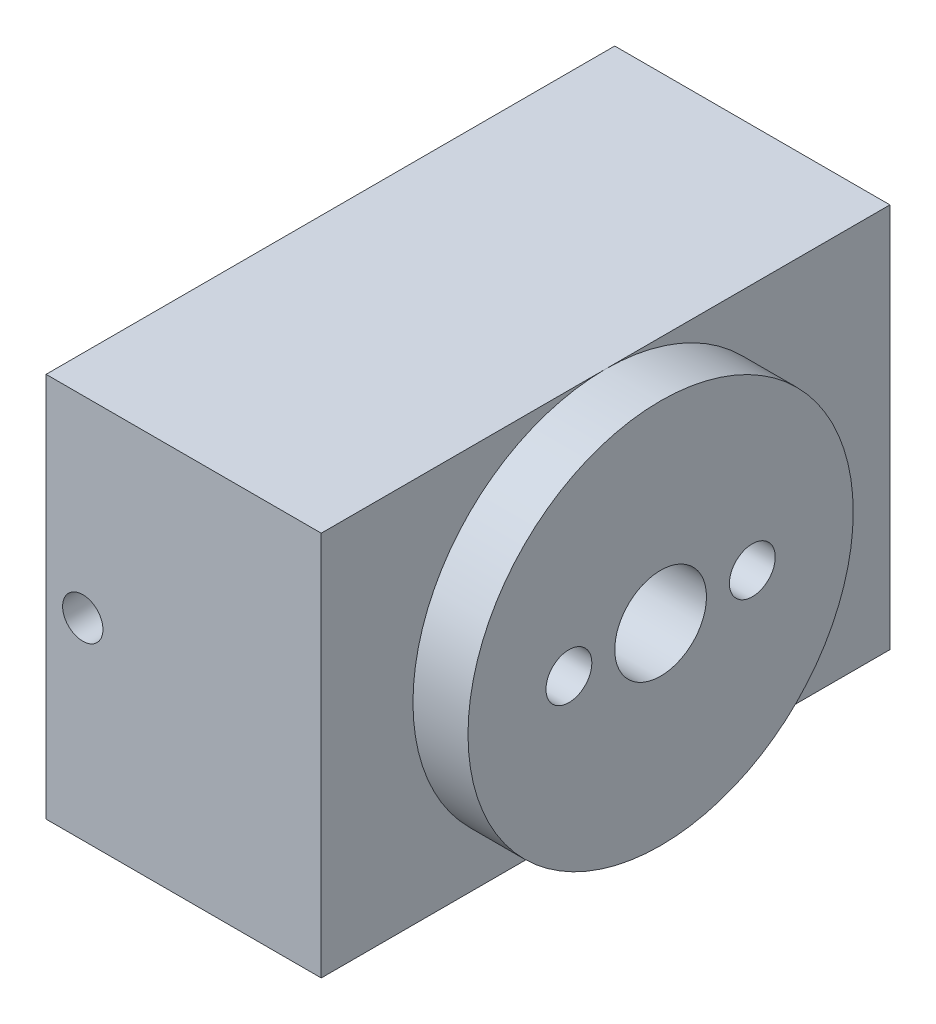
SolidWorks part; units mm, degrees
ref_plane "Front Plane" through (0, 0, 0) normal (0, 0, 1) x (1, 0, 0)
ref_plane "Top Plane" through (0, 0, 0) normal (0, 1, 0) x (1, 0, 0)
ref_plane "Right Plane" through (0, 0, 0) normal (1, 0, 0) x (0, 0, -1)
sketch "Sketch1" plane through (0, 0, 0) normal (1, 0, 0) x (0, 0, -1)
  line L0 (-15.5, 10.5) -> (15.5, 10.5)
  line L1 (-15.5, 10.5) -> (-15.5, -10.5)
  line L2 (-15.5, -10.5) -> (15.5, -10.5)
  line L3 (15.5, 10.5) -> (15.5, -10.5)
  dimension "D1" = 31
  dimension "D2" = 21
  dimension "D3" = 15.5
  dimension "D4" = 10.5
extrude "Boss-Extrude1" add sketch "Sketch1" along normal blind 15
sketch "Sketch4" plane through (0, 0, 15.5) normal (0, 0, 1) x (1, 0, 0)
  arc A0 (2.8122, 0.5833) -> (2.8122, -0.5833) centre (2, 0) ccw construction
  arc A1 (2.8122, 0.5833) -> (2.8122, -0.5833) centre (2, 0) ccw
  point P0 (2, 0)
hole_wizard "M2 Clearance Hole1" positions "Sketch4" profile "Sketch6" hole size "M2" standard "ANSI Metric" end condition through all
sketch "Sketch6" plane through (2, 0, 15.5) normal (1, 0, 0) x (0, -1, 0)
  line L0 (0, 0) -> (0, 31)
  line L1 (0, 31) -> (1.1, 31)
  line L2 (1.1, 31) -> (1.1, 0)
  line L5 (1.1, 0) -> (0, 0)
  line L11 (0, -6.35) -> (0, 107.95) construction
  dimension "Thru Hole Dia." = 2.2
  dimension "Thru Hole Depth" = 31
sketch "Sketch10" plane through (15, 0, 0) normal (1, 0, 0) x (0, 0, -1)
  circle A0 centre (0, 0) radius 10.5
extrude "Boss-Extrude3" add sketch "Sketch10" along normal blind 3
sketch "Sketch7" plane through (15, 0, 0) normal (1, 0, 0) x (0, 0, -1)
  circle A1 centre (-5, 0) radius 1.25
  circle A2 centre (5, 0) radius 1.25
  circle A3 centre (0, 0) radius 2.5
  dimension "D1" = 5
  dimension "D2" = 2.5
  dimension "D3" = 2.5
  dimension "D4" = 10
  dimension "D6" = 5
extrude "Cut-Extrude1" cut sketch "Sketch7" against normal through all both and the other way through all
equation "\"5c\"=5"
equation "\"2c\"=50"
